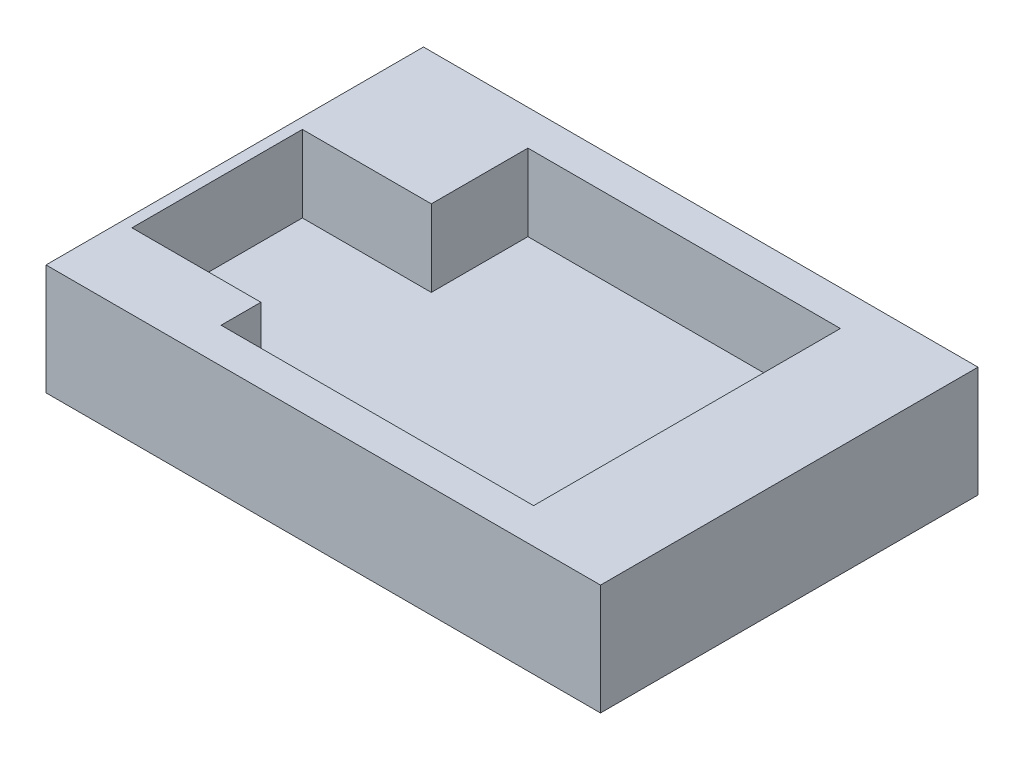
SolidWorks part; units mm, degrees
material "ABS"
ref_plane "Front Plane" through (0, 0, 0) normal (0, 0, 1) x (1, 0, 0)
ref_plane "Top Plane" through (0, 0, 0) normal (0, 1, 0) x (1, 0, 0)
ref_plane "Right Plane" through (0, 0, 0) normal (1, 0, 0) x (0, 0, -1)
sketch "Sketch1" plane through (0, 0, 0) normal (0, 1, 0) x (1, 0, 0)
  line L1 (48.8, 33.2187) -> (-48.8, 33.2187)
  line L2 (48.8, 33.2187) -> (48.8, -33.2187)
  line L3 (48.8, -33.2187) -> (-48.8, -33.2187)
  line L4 (-48.8, 33.2187) -> (-48.8, -33.2187)
  line L5 (48.8, 33.2187) -> (-48.8, -33.2187) construction
  line L6 (48.8, -33.2187) -> (-48.8, 33.2187) construction
  point P0 (0, 0)
  dimension "D1" = 97.6
  dimension "D2" = 66.4375
extrude "Boss-Extrude1" add sketch "Sketch1" along normal blind 6
sketch "Sketch3" plane through (0, 6, 0) normal (0, 1, 0) x (1, 0, 0)
  line L0 (48.8, -33.2187) -> (48.8, 33.2187) construction
  line L1 (30.8, 27) -> (-24.2, 27)
  line L2 (30.8, 27) -> (30.8, -27)
  line L3 (30.8, -27) -> (-24.2, -27)
  line L4 (-24.2, 27) -> (-24.2, -27)
  line L5 (30.8, 27) -> (-24.2, -27) construction
  line L6 (30.8, -27) -> (-24.2, 27) construction
  point P0 (3.3, 0)
  dimension "D1" = 54
  dimension "D2" = 55
  dimension "D3" = 0
  dimension "D4" = 18
sketch "Sketch4" plane through (0, 6, 0) normal (0, 1, 0) x (1, 0, 0)
  line L0 (30.8, -27) -> (30.8, -33.2187)
  line L1 (-48.8, -33.2187) -> (48.8, -33.2187) construction
  line L2 (30.8, -33.2187) -> (30.8, 33.2187)
  line L3 (48.8, 33.2187) -> (-48.8, 33.2187) construction
  line L4 (30.8, 33.2187) -> (30.8, 27)
  line L5 (30.8, 27) -> (48.8, 27)
  line L6 (48.8, -33.2187) -> (48.8, 33.2187) construction
  line L7 (48.8, 27) -> (-48.8, 27)
  line L8 (-48.8, 33.2187) -> (-48.8, -33.2187) construction
  line L9 (-48.8, 27) -> (-24.2, 27)
  line L10 (-24.2, 27) -> (-24.2, 33.2187)
  line L11 (-24.2, 33.2187) -> (-24.2, -33.2187)
  line L13 (-24.2, -33.2187) -> (-48.8, -33.2187)
  line L14 (-24.2, -33.2187) -> (-24.2, 33.2187)
  line L15 (-24.2, 33.2187) -> (-48.8, 33.2187)
  line L16 (-48.8, -33.2187) -> (-48.8, 33.2187)
  line L17 (-48.8, 33.2187) -> (48.8, 33.2187)
  line L18 (-48.8, 33.2187) -> (-48.8, 27)
  line L19 (-48.8, 27) -> (48.8, 27)
  line L20 (48.8, 33.2187) -> (48.8, 27)
  line L21 (48.8, 33.2187) -> (30.8, 33.2187)
  line L22 (48.8, 33.2187) -> (48.8, -33.2187)
  line L23 (48.8, -33.2187) -> (30.8, -33.2187)
  line L24 (30.8, 33.2187) -> (30.8, -33.2187)
  line L25 (48.8, -33.2187) -> (-48.8, -33.2187)
  line L26 (48.8, -33.2187) -> (48.8, -27)
  line L27 (48.8, -27) -> (-48.8, -27)
  line L28 (-48.8, -33.2187) -> (-48.8, -27)
  line M1 (-48.8, 33.2187) -> (-48.8, -33.2187)
  line M2 (-48.8, -33.2187) -> (48.8, -33.2187)
  line M3 (48.8, -33.2187) -> (48.8, 33.2187)
  line M4 (48.8, 33.2187) -> (-48.8, 33.2187)
extrude "Boss-Extrude2" add sketch "Sketch4" along normal blind 13.5 contours L27 L11 L7 M1 | L14 L27 L16 M2 | L0 L27 L14 M2 | L27 L0 M3 M2 | L27 L22 L5 L2 | L2 L5 M3 M4 | L7 L10 M4 M1 | L10 L7 L2 M4
sketch "Sketch5" plane through (0, 19.5, 0) normal (0, 1, 0) x (1, 0, 0)
  line L0 (-46.8936, -20) -> (-12.1997, -20)
  line L1 (-46.8936, -20) -> (-46.8936, 10)
  line L2 (-12.1997, -20) -> (-12.1997, 10)
  line L3 (-46.8936, 10) -> (-12.1997, 10)
  line L4 (-46.8936, -20) -> (-12.1997, 10) construction
  line L5 (-12.1997, -20) -> (-46.8936, 10) construction
  point P1 (-29.5467, -5)
  dimension "D1" = 30
  dimension "D2" = 5
extrude "Cut-Extrude1" cut sketch "Sketch5" against normal blind 13.5
